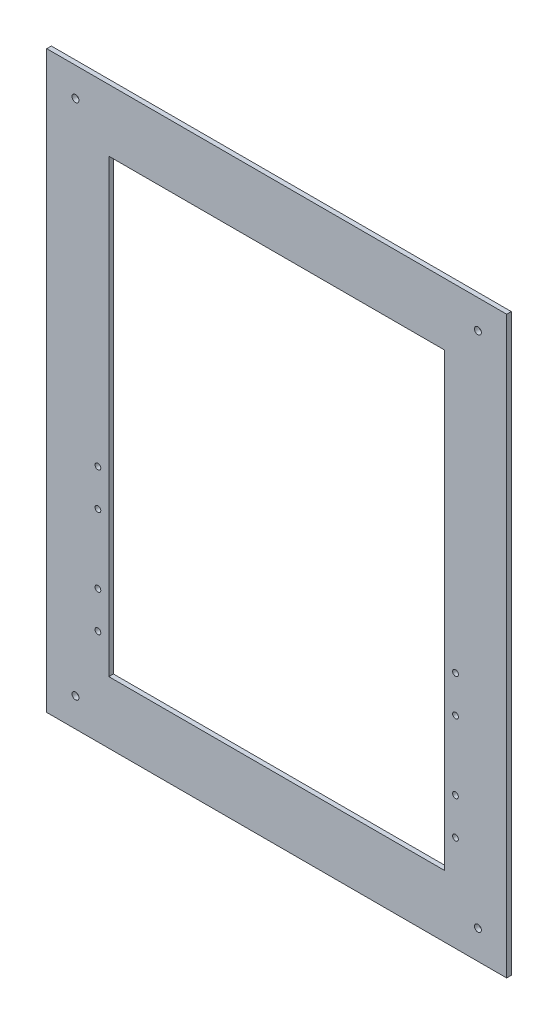
SolidWorks part; units mm, degrees
ref_plane "Plan de face" through (0, 0, 0) normal (0, 0, 1) x (1, 0, 0)
ref_plane "Plan de dessus" through (0, 0, 0) normal (0, 1, 0) x (1, 0, 0)
ref_plane "Plan de droite" through (0, 0, 0) normal (1, 0, 0) x (0, 0, -1)
sketch "Sketch1" plane through (0, 0, 0) normal (0, 0, 1) x (1, 0, 0)
  line L1 (0, 0) -> (400, 0)
  line L2 (0, 0) -> (0, 500)
  line L3 (0, 500) -> (400, 500)
  line L4 (400, 0) -> (400, 500)
  dimension "D1" = 500
  dimension "D2" = 400
extrude "Boss-Extrude1" add sketch "Sketch1" along normal blind 4
sketch "Sketch3" plane through (0, 0, 4) normal (0, 0, 1) x (1, 0, 0)
  line L0 (0, 0) -> (400, 0) construction
  line L1 (54, 446) -> (346, 446)
  line L2 (54, 446) -> (54, 54)
  line L3 (54, 54) -> (346, 54)
  line L4 (346, 446) -> (346, 54)
  line L5 (400, 500) -> (0, 500) construction
  line L6 (400, 0) -> (400, 500) construction
  line L8 (0, 500) -> (0, 0) construction
  dimension "D1" = 54
  dimension "D2" = 54
  dimension "D3" = 54
  dimension "D4" = 54
extrude "Cut-Extrude1" cut sketch "Sketch3" against normal up to body
sketch "Sketch4" plane through (0, 0, 0) normal (0, 0, -1) x (-1, 0, 0)
  line L0 (-54, 446) -> (-54, 54) construction
  line L1 (-54, 149.5) -> (0, 149.5) construction
  line L2 (0, 500) -> (0, 0) construction
  line L3 (-28, 223.5) -> (-55.51, 223.5) construction
  circle A0 centre (-45.34, 215.5) radius 2.5
  circle A1 centre (-38.4489, 184.2508) radius 2.5
  circle A2 centre (-38.4489, 114.7492) radius 2.5
  circle A3 centre (-45.34, 83.5) radius 2.5
  dimension "D1" = 5
  dimension "D2" = 5
  dimension "D3" = 8.66
  dimension "D4" = 15.5511
  dimension "D5" = 66
  dimension "D6" = 8
  dimension "D7" = 32
extrude "Cut-Extrude2" [suppressed] cut sketch "Sketch4" against normal up to surface (2 mm away)
sketch "Sketch6" plane through (0, 0, 4) normal (0, 0, 1) x (1, 0, 0)
  line L0 (0, 0) -> (400, 0) construction
  line L1 (346, 54) -> (346, 446) construction
  circle A0 centre (355.5, 83.5) radius 2.5
  circle A1 centre (355.5, 115.5) radius 2.5
  circle A2 centre (355.5, 175.5) radius 2.5
  circle A3 centre (355.5, 207.5) radius 2.5
  dimension "D1" = 5
  dimension "D2" = 5
  dimension "D3" = 5
  dimension "D4" = 5
  dimension "D5" = 83.5
  dimension "D6" = 32
  dimension "D7" = 60
  dimension "D8" = 32
  dimension "D9" = 9.5
extrude "Cut-Extrude3" cut sketch "Sketch6" against normal up to surface (4 mm away) up to face at (200, 250, 0)
ref_plane "Plane1" through (200, 0, 0) normal (1, 0, 0) x (0, 0, -1)
mirror "Mirror1" about plane through (200, 0, 0) normal (1, 0, 0) of "Cut-Extrude3"
sketch "Sketch7" plane through (0, 0, 4) normal (0, 0, 1) x (1, 0, 0)
  line L0 (0, 500) -> (0, 0) construction
  line L1 (0, 0) -> (400, 0) construction
  line L3 (400, 500) -> (0, 500) construction
  line L5 (400, 0) -> (400, 500) construction
  circle A0 centre (25, 25) radius 3
  circle A1 centre (25, 475) radius 3
  circle A2 centre (25, 25) radius 3
  circle A3 centre (25, 475) radius 3
  circle A4 centre (375, 475) radius 3
  circle A5 centre (375, 475) radius 3
  circle A6 centre (375, 25) radius 3
  circle A7 centre (375, 25) radius 3
  dimension "D1" = 6
  dimension "D6" = 6
  dimension "D8" = 6
  dimension "D12" = 6
  dimension "D2" = 25
  dimension "D3" = 25
  dimension "D4" = 25
  dimension "D5" = 25
  dimension "D7" = 25
  dimension "D9" = 25
  dimension "D10" = 25
  dimension "D11" = 25
extrude "Cut-Extrude4" cut sketch "Sketch7" against normal blind 4 contours A4 | A1 | A0 | A6
equation "\"D2@Sketch6\"=\"D1@Sketch6\""
equation "\"D3@Sketch6\"=\"D1@Sketch6\""
equation "\"D4@Sketch6\"=\"D1@Sketch6\""
